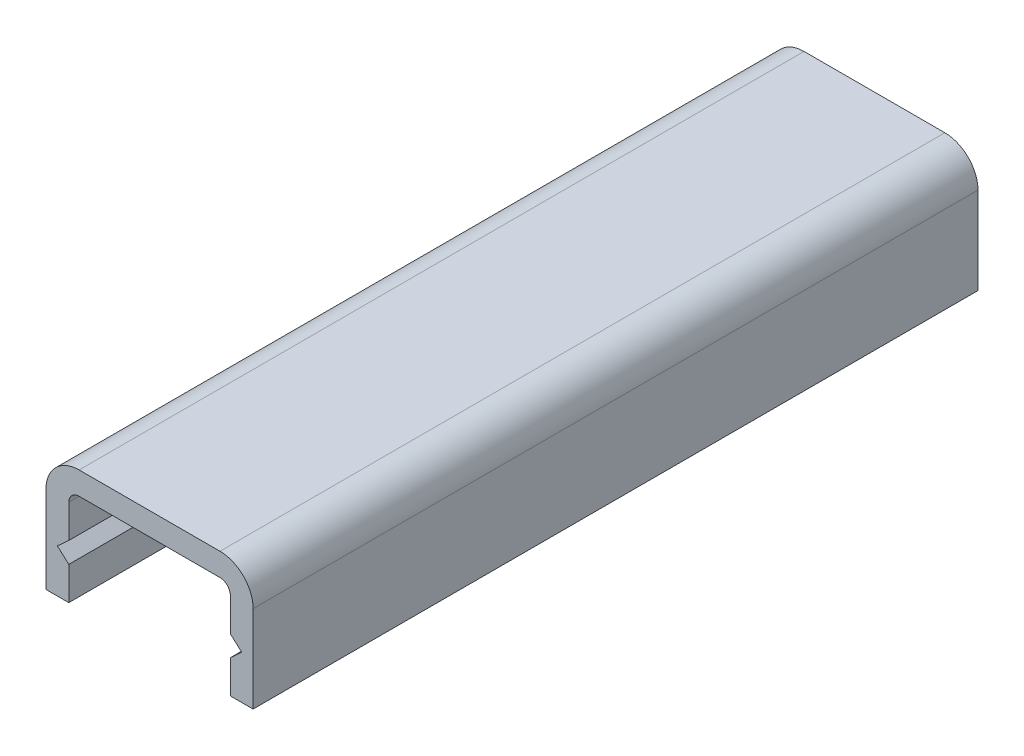
SolidWorks part; units mm, degrees
ref_plane "Plan de face" through (0, 0, 0) normal (0, 0, 1) x (1, 0, 0)
ref_plane "Plan de dessus" through (0, 0, 0) normal (0, 1, 0) x (1, 0, 0)
ref_plane "Plan de droite" through (0, 0, 0) normal (1, 0, 0) x (0, 0, -1)
sketch "Esquisse1" plane through (0, 0, 0) normal (0, 0, 1) x (1, 0, 0)
  line L0 (1.6, 0) -> (8.4, 0)
  line L1 (10, -1.6) -> (10, -5.8)
  line L2 (10, -5.8) -> (8.9, -5.8)
  line L3 (0, -1.6) -> (0, -5.8)
  line L5 (8.9, -1.6) -> (8.9, -3.2)
  line L6 (1.6, -1.1) -> (8.4, -1.1)
  line L7 (1.1, -1.6) -> (1.1, -3.2)
  line L8 (0, -5.8) -> (1.1, -5.8)
  line L9 (8.9, -1.1) -> (8.9, -4.7) construction
  line L10 (0, 0) -> (10, 0) construction
  line L11 (0, 0) -> (0, -5.8) construction
  line L12 (1.1, -1.1) -> (8.9, -1.1) construction
  line L13 (1.1, -1.1) -> (1.1, -5.8) construction
  line L14 (10, 0) -> (10, -5.8) construction
  line L15 (1.1, -4.2) -> (1.1, -5.8)
  line L16 (1.1, -4.2) -> (0.55, -3.7)
  line L17 (8.9, -4.2) -> (8.9, -5.8)
  line L18 (1.1, -3.2) -> (0.55, -3.7)
  line L19 (8.9, -3.2) -> (9.45, -3.7)
  line L20 (8.9, -4.2) -> (9.45, -3.7)
  line L21 (8.9, -4.7) -> (8.9, -4.7) construction
  arc A1 (1.6, -1.1) -> (1.1, -1.6) centre (1.6, -1.6) ccw
  arc A2 (8.9, -1.6) -> (8.4, -1.1) centre (8.4, -1.6) ccw
  arc A3 (8.4, 0) -> (10, -1.6) centre (8.4, -1.6) cw
  arc A4 (0, -1.6) -> (1.6, 0) centre (1.6, -1.6) cw
  dimension "D3" = 1.6
  dimension "D1" = 1.1
extrude "Extrusion1" add sketch "Esquisse1" along normal blind 35
